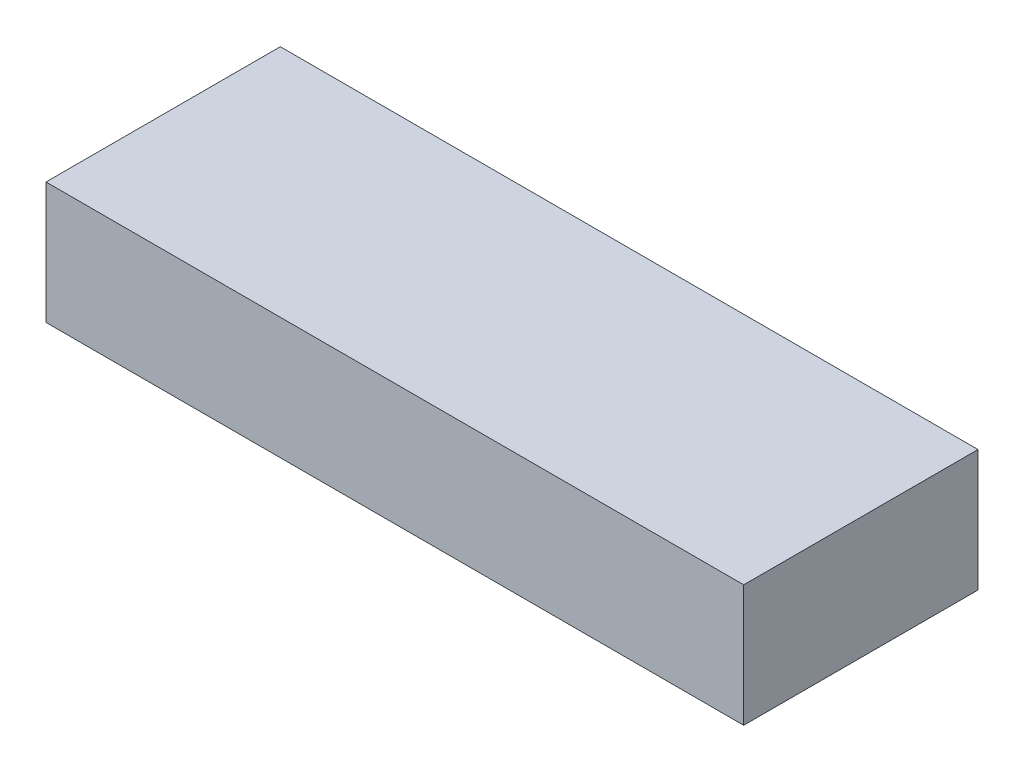
SolidWorks part; units mm, degrees
ref_plane "Front Plane" through (0, 0, 0) normal (0, 0, 1) x (1, 0, 0)
ref_plane "Top Plane" through (0, 0, 0) normal (0, 1, 0) x (1, 0, 0)
ref_plane "Right Plane" through (0, 0, 0) normal (1, 0, 0) x (0, 0, -1)
sketch "Sketch2" plane through (0, 0, 0) normal (0, 1, 0) x (1, 0, 0)
  line L1 (-68.453, 22.987) -> (68.453, 22.987)
  line L2 (-68.453, 22.987) -> (-68.453, -22.987)
  line L3 (-68.453, -22.987) -> (68.453, -22.987)
  line L4 (68.453, 22.987) -> (68.453, -22.987)
  line L5 (-68.453, 22.987) -> (68.453, -22.987) construction
  line L6 (-68.453, -22.987) -> (68.453, 22.987) construction
  point P0 (0, 0)
  dimension "D1" = 136.906
  dimension "D2" = 45.974
extrude "Boss-Extrude1" add sketch "Sketch2" along normal blind 23.876
